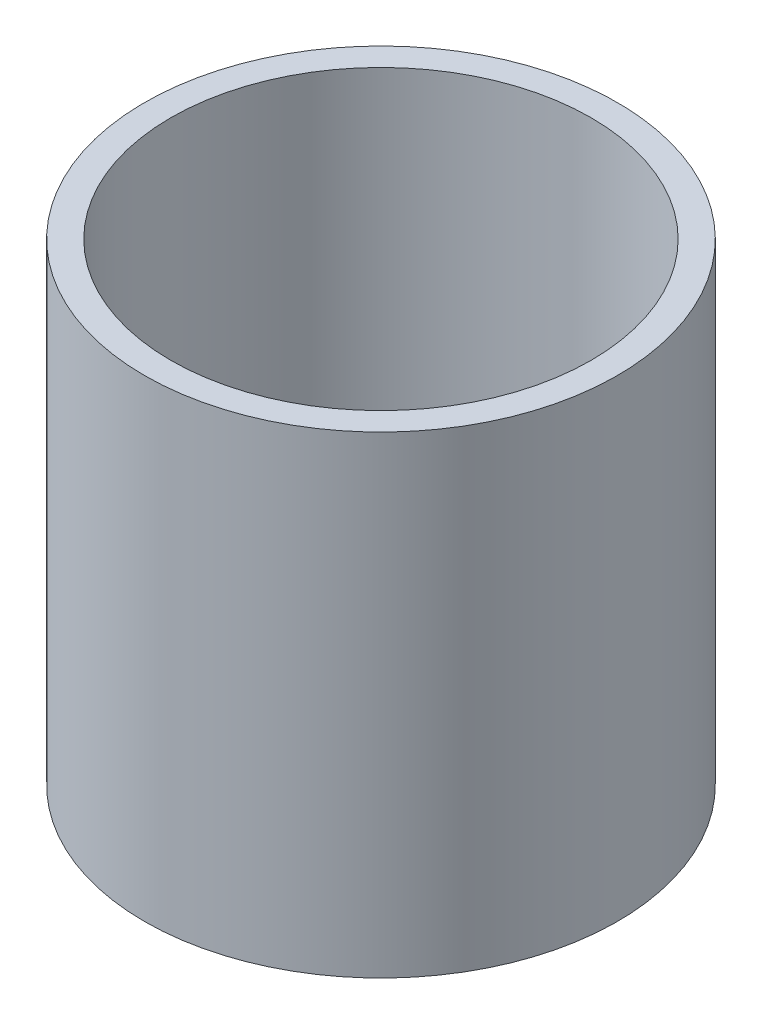
SolidWorks part; units mm, degrees
ref_plane "Front Plane" through (0, 0, 0) normal (0, 0, 1) x (1, 0, 0)
ref_plane "Top Plane" through (0, 0, 0) normal (0, 1, 0) x (1, 0, 0)
ref_plane "Right Plane" through (0, 0, 0) normal (1, 0, 0) x (0, 0, -1)
sketch "Sketch1" plane through (0, 0, 0) normal (0, 1, 0) x (1, 0, 0)
  circle A0 centre (0, 0) radius 9
  dimension "D1" = 18
extrude "Boss-Extrude1" add sketch "Sketch1" along normal blind 18
shell "Shell1" thickness 1
equation "\"L\" = 18"
equation "\"D1@Sketch1\"=\"L\""
equation "\"D1@Boss-Extrude1\"=\"L\""
